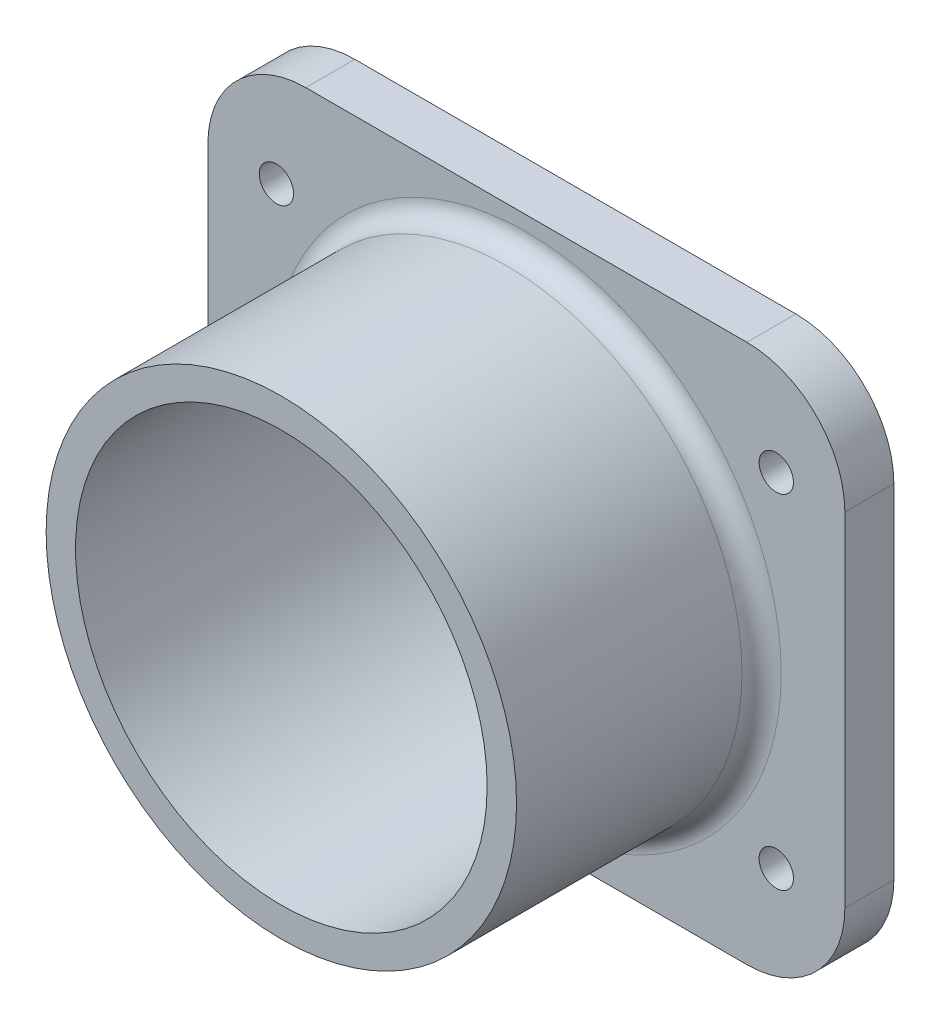
SolidWorks part; units mm, degrees
ref_plane "前视基准面" through (0, 0, 0) normal (0, 0, 1) x (1, 0, 0)
ref_plane "上视基准面" through (0, 0, 0) normal (0, 1, 0) x (1, 0, 0)
ref_plane "右视基准面" through (0, 0, 0) normal (1, 0, 0) x (0, 0, -1)
sketch "草图1" plane through (0, 0, 0) normal (0, 0, 1) x (1, 0, 0)
  circle A0 centre (0, 0) radius 27.5
  circle A1 centre (0, 0) radius 20 construction
  dimension "D1" = 55
  dimension "D2" = 40
extrude "凸台-拉伸1" add sketch "草图1" along normal blind 5
sketch "草图2" plane through (0, 0, 5) normal (0, 0, 1) x (1, 0, 0)
  circle A0 centre (0, 0) radius 24
  dimension "D1" = 48
extrude "凸台-拉伸2" add sketch "草图2" along normal blind 25
sketch "草图4" plane through (0, 0, 0) normal (0, 0, -1) x (-1, 0, 0)
  line L1 (32.5, -27.5) -> (-32.5, -27.5)
  line L2 (32.5, -27.5) -> (32.5, 27.5)
  line L3 (32.5, 27.5) -> (-32.5, 27.5)
  line L4 (-32.5, -27.5) -> (-32.5, 27.5)
  line L5 (0, 27.5) -> (0, -27.5) construction
  line L6 (32.5, 0) -> (-32.5, 0) construction
  circle A0 centre (0, 0) radius 27.5 construction
  circle A1 centre (0, 0) radius 27.5 construction
  dimension "D1" = 65
extrude "凸台-拉伸3" add sketch "草图4" against normal blind 5
sketch "草图5" plane through (0, 0, 30) normal (0, 0, 1) x (1, 0, 0)
  circle A0 centre (0, 0) radius 21
  dimension "D1" = 42
extrude "切除-拉伸1" cut sketch "草图5" against normal blind 59
fillet "圆角1" radius 10 4 edges at (32.5, 27.5, 2.5) (32.5, -27.5, 2.5) (-32.5, -27.5, 2.5) (-32.5, 27.5, 2.5)
sketch "草图6" plane through (0, 0, 5) normal (0, 0, 1) x (1, 0, 0)
  line L0 (0, 0) -> (-32.5, 0) construction
  line L1 (-32.5, -17.5) -> (-32.5, 17.5) construction
  line L2 (0, 0) -> (0, -27.5) construction
  line L3 (22.5, -27.5) -> (-22.5, -27.5) construction
  circle A0 centre (-25.5, -17.5) radius 1.75
  circle A1 centre (-25.5, 17.5) radius 1.75
  circle A2 centre (25.5, 17.5) radius 1.75
  circle A3 centre (25.5, -17.5) radius 1.75
  dimension "D1" = 3.5
  dimension "D2" = 35
  dimension "D3" = 51
extrude "切除-拉伸2" cut sketch "草图6" against normal blind 10
fillet "圆角2" radius 2 1 edges at (24, 0, 5)
